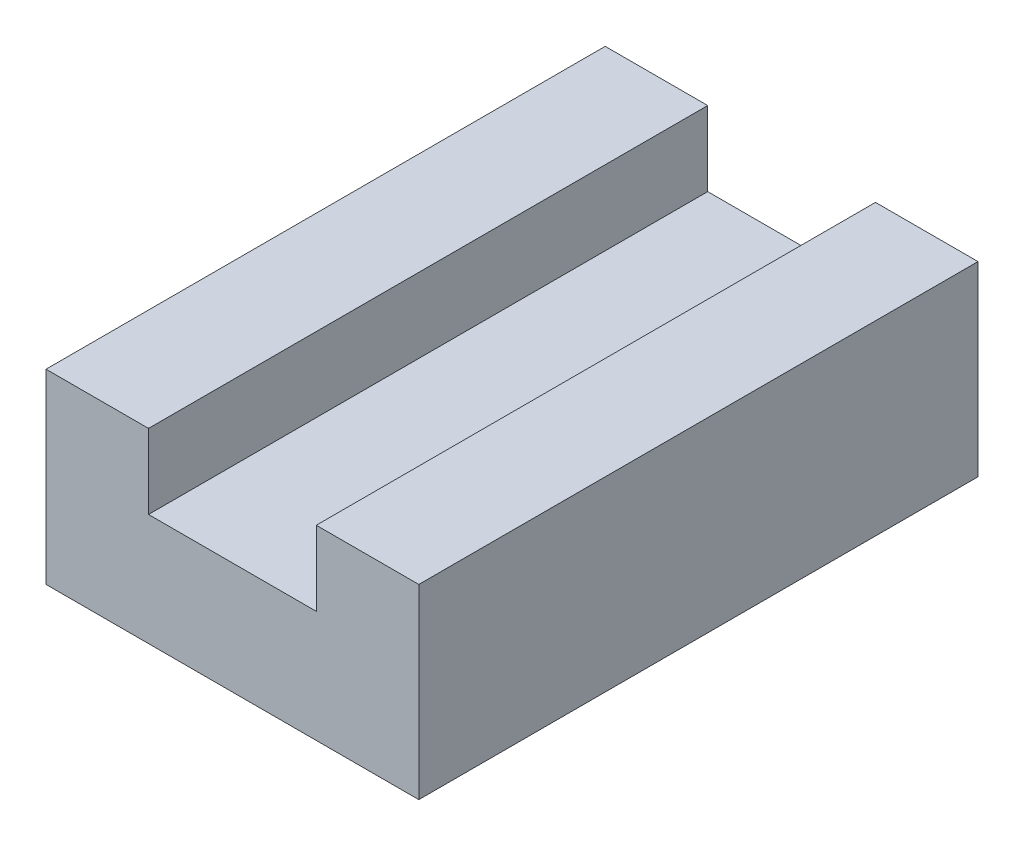
SolidWorks part; units mm, degrees
ref_plane "Front Plane" through (0, 0, 0) normal (0, 0, 1) x (1, 0, 0)
ref_plane "Top Plane" through (0, 0, 0) normal (0, 1, 0) x (1, 0, 0)
ref_plane "Right Plane" through (0, 0, 0) normal (1, 0, 0) x (0, 0, -1)
sketch "Sketch1" plane through (0, 0, 0) normal (0, 1, 0) x (1, 0, 0)
  line L1 (0, 0) -> (20, 0)
  line L2 (0, 0) -> (0, 30)
  line L3 (0, 30) -> (20, 30)
  line L4 (20, 0) -> (20, 30)
  dimension "D1" = 20
  dimension "D2" = 30
extrude "Boss-Extrude1" add sketch "Sketch1" along normal blind 10
sketch "Sketch2" plane through (0, 0, 0) normal (0, 0, 1) x (1, 0, 0)
  line L0 (0, 10) -> (20, 10) construction
  line L1 (5.5, 10) -> (14.5, 10)
  line L2 (5.5, 10) -> (5.5, 6)
  line L3 (5.5, 6) -> (14.5, 6)
  line L4 (14.5, 10) -> (14.5, 6)
  line L5 (10, 10) -> (10, 0) construction
  line L6 (0, 0) -> (20, 0) construction
  dimension "D1" = 9
  dimension "D2" = 4
extrude "Cut-Extrude1" cut sketch "Sketch2" against normal through all
sketch "Sketch3" plane through (0, 0, 0) normal (0, -1, 0) x (1, 0, 0)
  line L0 (10, -30) -> (10, 0) construction
  line L1 (20, -30) -> (0, -30) construction
  line L2 (0, 0) -> (20, 0) construction
  circle A0 centre (2.5, -19.6821) radius 1.5
  circle A1 centre (17.5, -19.6821) radius 1.5
  circle A2 centre (17.5, -9.6821) radius 1.5
  circle A3 centre (2.5, -9.6821) radius 1.5
  dimension "D1" = 3
  dimension "D2" = 3
  dimension "D3" = 3
  dimension "D4" = 3
  dimension "D5" = 10
  dimension "D6" = 15
extrude "Cut-Extrude2" cut sketch "Sketch3" against normal blind 5
